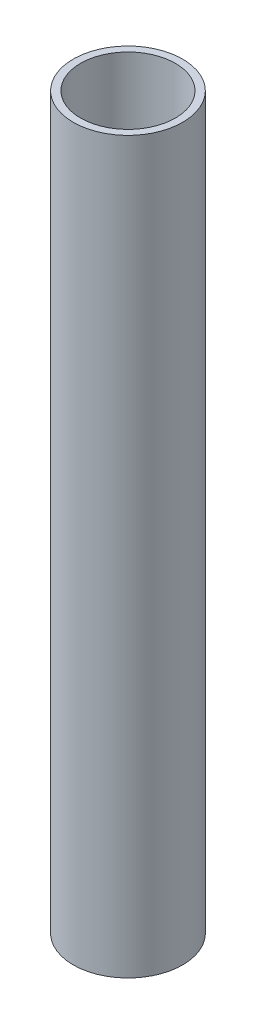
SolidWorks part; units mm, degrees
material "3.1355 (EN-AW 2024)"
ref_plane "Front" through (0, 0, 0) normal (0, 0, 1) x (1, 0, 0)
ref_plane "Top" through (0, 0, 0) normal (0, 1, 0) x (1, 0, 0)
ref_plane "Right" through (0, 0, 0) normal (1, 0, 0) x (0, 0, -1)
sketch "Эскиз1" plane through (0, 0, 0) normal (0, 1, 0) x (1, 0, 0)
  circle A0 centre (0, 0) radius 7.5
  circle A1 centre (0, 0) radius 6.5
  dimension "D1" = 15
  dimension "D2" = 13
extrude "Бобышка-Вытянуть1" add sketch "Эскиз1" along normal blind 100
